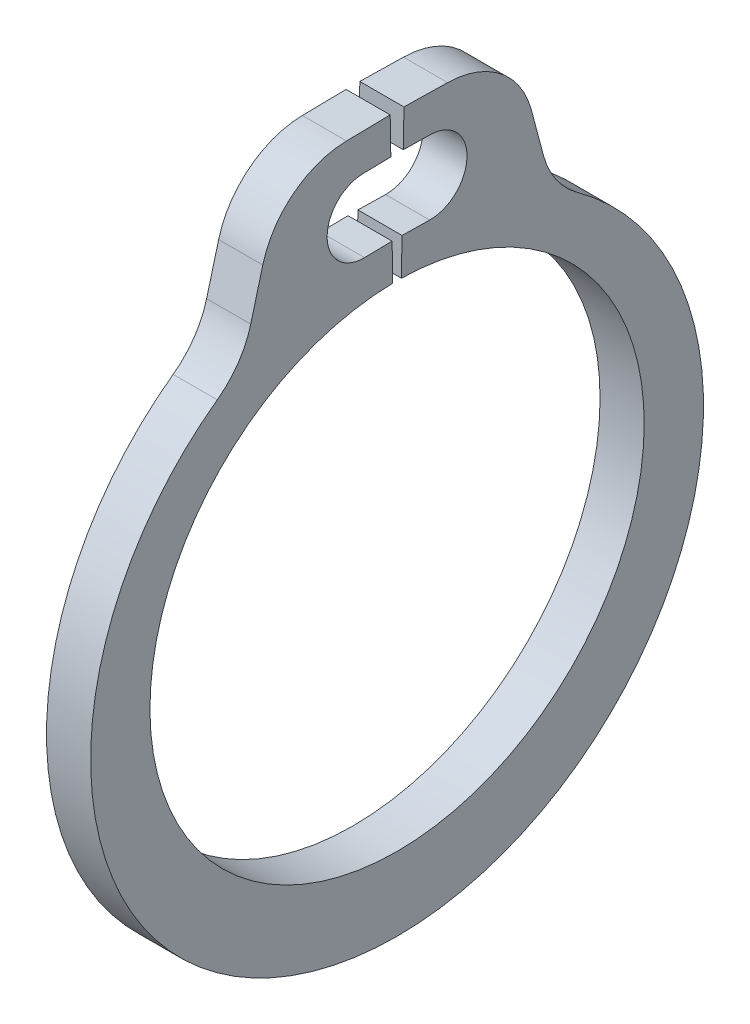
SolidWorks part; units mm, degrees
material "Cast Carbon Steel"
ref_plane "Front" through (0, 0, 0) normal (0, 0, 1) x (1, 0, 0)
ref_plane "Top" through (0, 0, 0) normal (0, 1, 0) x (1, 0, 0)
ref_plane "Right" through (0, 0, 0) normal (1, 0, 0) x (0, 0, -1)
sketch "Sketch1" plane through (0, 0, 0) normal (1, 0, 0) x (0, 0, -1)
  line L0 (0, 0) -> (0, 2.1336) construction
  line L1 (-0.0372, 2.1333) -> (-0.0594, 3.4031) construction
  line L2 (0.0594, 3.4031) -> (1.0118, 3.3865)
  line L3 (1.0118, 3.3865) -> (1.3379, 2.1591)
  line L4 (0.0372, 2.1333) -> (0.0594, 3.4031) construction
  line L5 (-0.0594, 3.4031) -> (-1.0118, 3.3865)
  line L6 (-1.0118, 3.3865) -> (-1.3379, 2.1591)
  line L7 (-1.3379, 2.1591) -> (-1.1239, 1.8136) construction
  line L8 (1.3379, 2.1591) -> (1.1239, 1.8136) construction
  line L9 (0, -2.1336) -> (0, -2.7686) construction
  line L10 (-1.0118, 3.3865) -> (-0.0372, 2.1333) construction
  line L11 (0, 2.1336) -> (0, 3.4036) construction
  line L12 (0.0428, 2.4507) -> (0.2809, 2.4466)
  line L13 (0.0539, 3.0856) -> (0.2919, 3.0815)
  line L14 (0.0428, 2.4507) -> (0.0372, 2.1333)
  line L15 (0.0539, 3.0856) -> (0.0594, 3.4031)
  line L16 (-0.0539, 3.0856) -> (-0.2919, 3.0815)
  line L17 (-0.0428, 2.4507) -> (-0.2809, 2.4466)
  line L18 (-0.0428, 2.4507) -> (-0.0372, 2.1333)
  line L19 (-0.0539, 3.0856) -> (-0.0594, 3.4031)
  line L20 (-2.1336, 0) -> (2.1336, 0) construction
  circle A0 centre (0, 0) radius 2.1336 construction
  arc A1 (-0.0372, 2.1333) -> (0.0372, 2.1333) centre (0, 0) ccw
  arc A2 (0.2809, 2.4466) -> (0.2919, 3.0815) centre (0.2864, 2.764) ccw
  circle A3 centre (0, 0) radius 3.7846 construction
  arc A4 (-0.2809, 2.4466) -> (-0.2919, 3.0815) centre (-0.2864, 2.764) cw
  arc A6 (-1.3379, 2.1591) -> (1.3379, 2.1591) centre (0, -0.1231) ccw
  point P0 (0, -2.7686)
  dimension "A" = 4.2672
  dimension "Smin" = 0.4064
  dimension "H" = 1.27
  dimension "D2" = 0.9525
  dimension "Angle" = 1
  dimension "R" = 0.635
extrude "Extrude1" add sketch "Sketch1" along normal mid plane 0.381
fillet "Fillet1" radius 0.762 4 edges at (0, 2.1591, 1.3379) (0, 2.1591, -1.3379) (0, 3.3865, 1.0118) (0, 3.3865, -1.0118)
sketch "Sketch2" plane through (0, 0, 0) normal (0, 0, 1) x (1, 0, 0)
  line L0 (-2.1336, 0) -> (5.4864, 0)
  line L1 (5.4864, 0) -> (5.4864, -2.3812)
  line L2 (-0.2286, -2.3812) -> (-1.9748, -2.3812)
  line L3 (5.4864, -2.3812) -> (0.2286, -2.3812)
  line L4 (0.2286, -2.3812) -> (0.2286, -2.2225)
  line L5 (0.2286, -2.2225) -> (-0.2286, -2.2225)
  line L6 (-0.2286, -2.2225) -> (-0.2286, -2.3812)
  line L7 (-0.2286, -2.3812) -> (-2.1336, -2.3812) construction
  line L8 (-2.1336, -2.3812) -> (-2.1336, 0) construction
  line L9 (5.4864, 0) -> (76.391, 0) construction
  line L10 (-1.9748, -2.3812) -> (-2.1336, -2.2225)
  line L11 (-2.1336, -2.2225) -> (-2.1336, 0)
  point P10 (0, -2.2225)
  dimension "D2" = 7.62
  dimension "D3" = 1.905
  dimension "D1" = 45
revolve "Revolve1" [suppressed] add sketch "Sketch2" angle 360 about L9
delete or keep bodies "Body-Delete1" [suppressed] type delete bodies bodies 122
equation "\"D2@Sketch2\" = \"D1@Extrude1\"*20"
equation "\"D3@Sketch2\" = \"D2@Sketch2\"/4"
equation "\"D2@Sketch1\" = \"H@Sketch1\"*.75"
equation "\"D1@Fillet1\" = \"D1@Extrude1\"*2"
